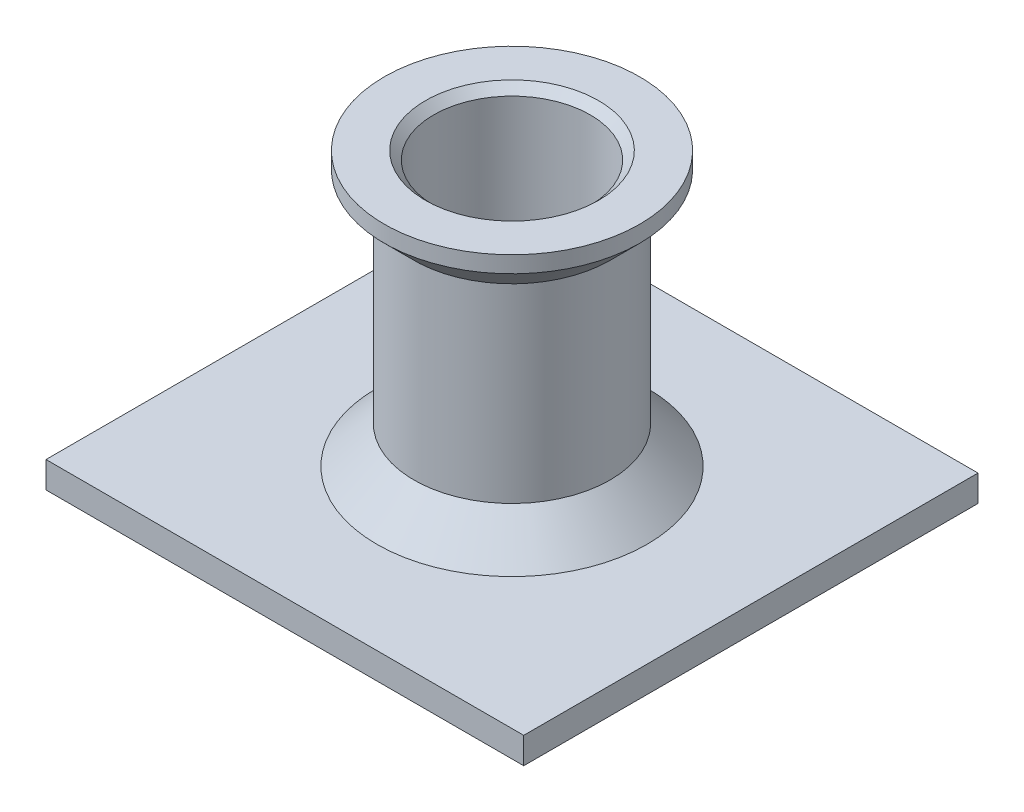
SolidWorks part; units mm, degrees
ref_plane "Front Plane" through (0, 0, 0) normal (0, 0, 1) x (1, 0, 0)
ref_plane "Top Plane" through (0, 0, 0) normal (0, 1, 0) x (1, 0, 0)
ref_plane "Right Plane" through (0, 0, 0) normal (1, 0, 0) x (0, 0, -1)
sketch "Sketch1" plane through (0, 0, 0) normal (0, 0, 1) x (1, 0, 0)
  line L0 (0, -12.9233) -> (0, 12.9233) construction
  line L1 (-19.3603, 0) -> (19.3603, 0) construction
  line L2 (4.75, 9.5) -> (4.75, 0)
  line L3 (5.25, 10) -> (7.75, 10)
  line L4 (7.75, 10) -> (7.75, 9)
  line L5 (7.75, 9) -> (5.95, 7.2)
  line L8 (5.95, 7.2) -> (5.95, -4.3426)
  line L9 (4.75, 9.5) -> (5.25, 10)
  line L13 (3.25, -8.1935) -> (3.25, -1.5)
  line L14 (3.25, -1.5) -> (4.75, 0)
  line L15 (8.2008, -6.5935) -> (20, -6.5935)
  line L16 (20, -6.5935) -> (20, -8.1935)
  line L18 (20, -8.1935) -> (3.25, -8.1935)
  line L19 (8.2008, -6.5935) -> (5.95, -4.3426)
  point P0 (4.75, 10)
  point P4 (0, 0)
  point P7 (0, 0)
  point P9 (5.95, 0)
  dimension "D1" = 4.75
  dimension "D2" = 3
  dimension "D3" = 10
  dimension "D4" = 1
  dimension "D5" = 5.95
  dimension "D6" = 45
  dimension "D7" = 45
  dimension "D8" = 45
  dimension "D9" = 1.6
  dimension "D10" = 3.25
  dimension "D12" = 20
revolve "Revolve1" add sketch "Sketch1" angle 360 about L0
sketch "Sketch2" plane through (0, 0, 0) normal (0, 1, 0) x (1, 0, 0)
  line L1 (-14.4934, 13.7819) -> (14.4934, 13.7819)
  line L2 (-14.4934, 13.7819) -> (-14.4934, -13.7819)
  line L3 (-14.4934, -13.7819) -> (14.4934, -13.7819)
  line L4 (14.4934, 13.7819) -> (14.4934, -13.7819)
  line L5 (-14.4934, 13.7819) -> (14.4934, -13.7819) construction
  line L6 (-14.4934, -13.7819) -> (14.4934, 13.7819) construction
  circle A0 centre (0, 0) radius 20 construction
  point P0 (0, 0)
extrude "Cut-Extrude1" cut sketch "Sketch2" against normal through all both and the other way through all flip side to cut
